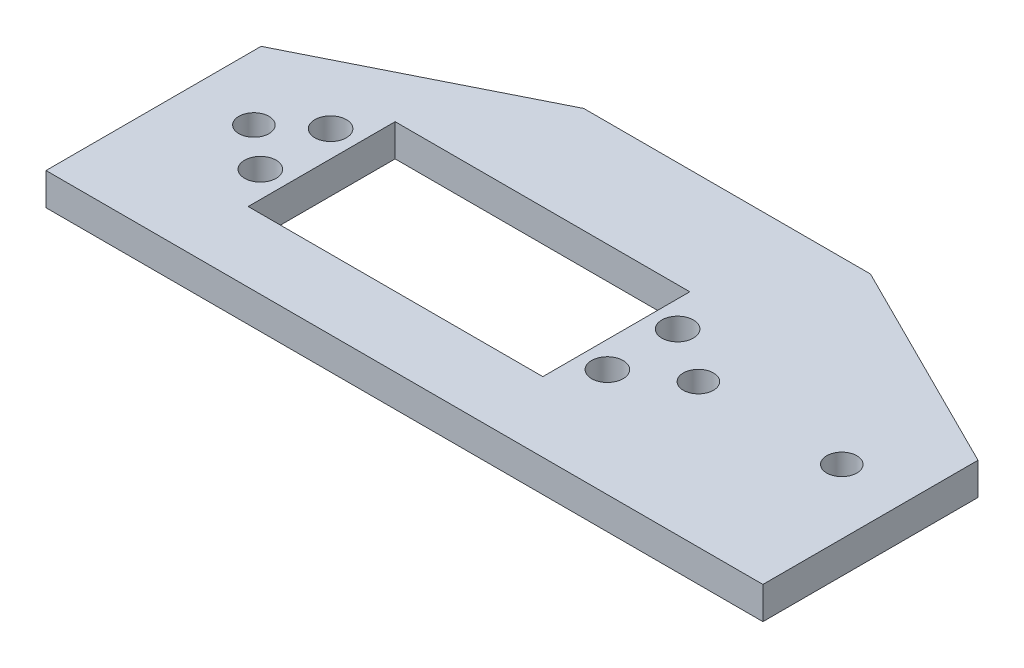
SolidWorks part; units mm, degrees
ref_plane "Front Plane" through (0, 0, 0) normal (0, 0, 1) x (1, 0, 0)
ref_plane "Top Plane" through (0, 0, 0) normal (0, 1, 0) x (1, 0, 0)
ref_plane "Right Plane" through (0, 0, 0) normal (1, 0, 0) x (0, 0, -1)
sketch "Sketch1" plane through (0, 0, 0) normal (0, 1, 0) x (1, 0, 0)
  line L0 (20, 40) -> (50, 25)
  line L1 (-20, 40) -> (-50, 25)
  line L2 (-50, 25) -> (-50, -25)
  line L3 (-50, -25) -> (50, -25)
  line L4 (50, 25) -> (50, -25)
  line L5 (-50, 25) -> (50, -25) construction
  line L6 (-50, -25) -> (50, 25) construction
  line L7 (-20, 40) -> (20, 40)
  circle A0 centre (-41, 15) radius 2.1
  circle A1 centre (41, 15) radius 2.1
  circle A2 centre (-21, 15) radius 2.1
  circle A3 centre (21, 15) radius 2.1
  point P0 (0, 0)
  dimension "D3" = 4.2
  dimension "D4" = 4.2
  dimension "D6" = 20
  dimension "D7" = 4.2
  dimension "D8" = 4.2
  dimension "D1" = 100
  dimension "D2" = 50
  dimension "D5" = 82
  dimension "D9" = 20
  dimension "D10" = 40
  dimension "D11" = 21
extrude "Boss-Extrude1" add sketch "Sketch1" along normal blind 4.5
sketch "Sketch2" plane through (0, 0, 0) normal (0, -1, 0) x (1, 0, 0)
  line L0 (-31.55, -4.75) -> (9.55, -4.75)
  line L1 (9.55, -4.75) -> (9.55, -25.25)
  line L2 (9.55, -25.25) -> (-31.55, -25.25)
  line L3 (-31.55, -25.25) -> (-31.55, -4.75)
  line L4 (-31.1, -5) -> (9.1, -5) construction
  line L9 (-31.3, -24.8) -> (-31.3, -5.2) construction
  line L10 (9.1, -25) -> (-31.1, -25) construction
  line L11 (9.3, -5.2) -> (9.3, -24.8) construction
  circle A0 centre (13.2, -19.9) radius 2.2
  circle A1 centre (13.2, -10.1) radius 2.2
  circle A2 centre (-35.2, -19.9) radius 2.2
  circle A3 centre (-35.2, -10.1) radius 2.2
  dimension "D1" = 0.25
  dimension "D2" = 0.25
  dimension "D3" = 0.25
  dimension "D4" = 0.25
extrude "Cut-Extrude1" cut sketch "Sketch2" against normal blind 10
sketch "Sketch3" plane through (0, 0, 0) normal (0, -1, 0) x (1, 0, 0)
  line L0 (50, 25) -> (50, -25) construction
  line L1 (50, 25) -> (-50, 25)
  line L2 (50, 25) -> (50, 5)
  line L3 (50, 5) -> (-50, 5)
  line L4 (-50, 25) -> (-50, 5)
  dimension "D2" = 20
extrude "Cut-Extrude2" cut sketch "Sketch3" against normal blind 10
